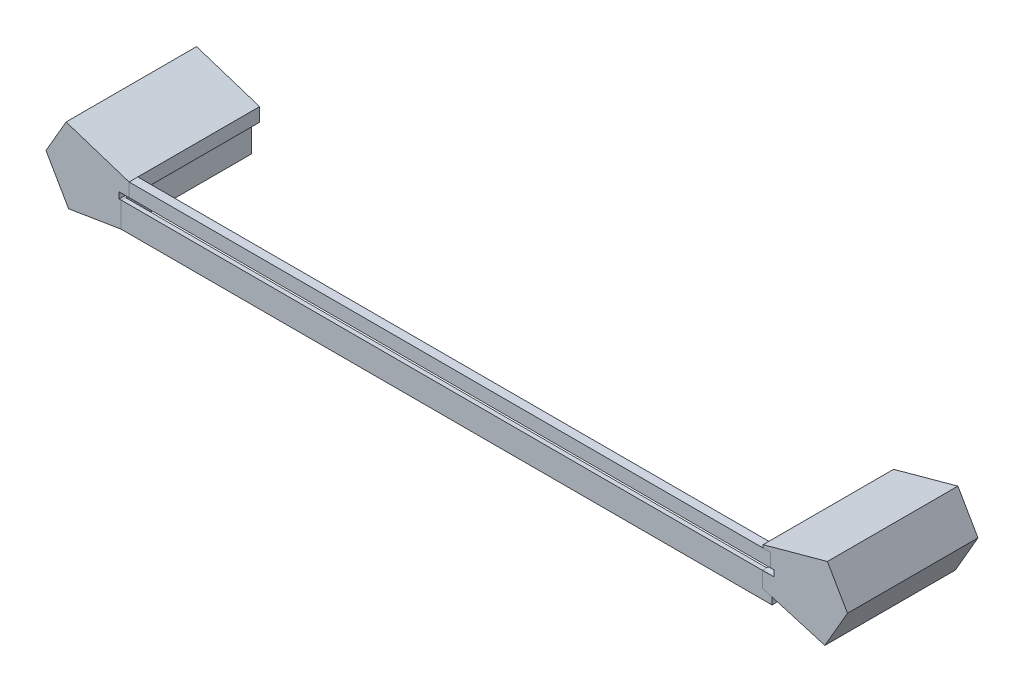
SolidWorks part; units mm, degrees
ref_plane "Plano frontal" through (0, 0, 0) normal (0, 0, 1) x (1, 0, 0)
ref_plane "Plano superior" through (0, 0, 0) normal (0, 1, 0) x (1, 0, 0)
ref_plane "Plano direito" through (0, 0, 0) normal (1, 0, 0) x (0, 0, -1)
sketch "Esboço1" plane through (0, 0, 0) normal (0, 0, 1) x (1, 0, 0)
  line L0 (-92.11, 0) -> (-87.4912, 8)
  line L4 (-86.9138, -9) -> (-92.11, 0)
  line L5 (-92.11, 0) -> (92.11, 0) construction
  line L6 (92.11, 0) -> (87.4912, 8)
  line L7 (-74.8409, -7.025) -> (-74.8409, -1.2263)
  line L8 (-74.8409, -1.2263) -> (-75.2754, -1.2268)
  line L9 (-75.2754, -1.2268) -> (-75.2771, 0.1732)
  line L10 (-75.2771, 0.1732) -> (-73.015, 0.1759)
  line L11 (-73.015, 0.1759) -> (-73.015, 3.2887)
  line L15 (-92.11, 0) -> (-92.11, -8.8202) construction
  line L16 (-74.8409, -7.025) -> (-86.9138, -9)
  line L17 (-73.015, 3.2887) -> (-87.4912, 8)
  line L18 (87.4912, 8) -> (72.7082, 3.9537)
  line L19 (72.7082, 3.9537) -> (72.7082, 0.2083)
  line L20 (72.7082, 0.2083) -> (75.2769, 0.2083)
  line L21 (75.2769, 0.2083) -> (75.2769, -1.1917)
  line L22 (75.2769, -1.1917) -> (72.5621, -1.1917)
  line L23 (72.5621, -1.1917) -> (72.5621, -4.7894)
  line L24 (72.5621, -4.7894) -> (86.9138, -9)
  line L25 (86.9138, -9) -> (92.11, 0)
  line L26 (92.11, 0) -> (92.11, -19.0701) construction
  point P14 (0, 0)
  point P22 (73.557, 4.4671)
  point P23 (72.1777, -9.9666)
  point P24 (66.7523, 2.3235)
  point P25 (0, 0)
  point P26 (72.5621, -4.7894)
  dimension "D1" = 1.4
  dimension "D2" = 30
  dimension "D3" = 120
  dimension "D4" = 120
  dimension "D5" = 30
  dimension "D6" = 16.8331
  dimension "D7" = 184.22
  dimension "D8" = 8
  dimension "D9" = 9
  dimension "D10" = 8
  dimension "D11" = 9
  dimension "D12" = 16.8331
  dimension "D13" = 1.4
extrude "Ressalto-extrusão1" add sketch "Esboço1" along normal blind 30
sketch "Esboço2" plane through (0, 0, 30) normal (0, 0, 1) x (1, 0, 0)
  line L1 (-73.015, 0.1759) -> (74.4295, 0.1759)
  line L2 (74.4295, 0.1759) -> (74.4295, 3.2887)
  line L3 (74.4295, 3.2887) -> (-73.015, 3.2887)
  line L4 (-73.015, 0.1759) -> (-73.015, 3.2887) construction
  line L5 (-73.015, 3.2887) -> (-73.015, 0.1759)
  point P0 (-74.7828, 2.1002)
extrude "Ressalto-extrusão2" add sketch "Esboço2" against normal blind 2 separate body
sketch "Esboço3" plane through (0, 0, 30) normal (0, 0, 1) x (1, 0, 0)
  line L1 (-74.8409, -1.2263) -> (74.771, -1.2263)
  line L2 (-74.8409, -1.2263) -> (-74.8409, -7.025)
  line L3 (-74.8409, -7.025) -> (74.771, -7.025)
  line L4 (74.771, -1.2263) -> (74.771, -7.025)
  point P5 (-75.9037, -6.513)
extrude "Ressalto-extrusão3" add sketch "Esboço3" against normal blind 1 separate body
